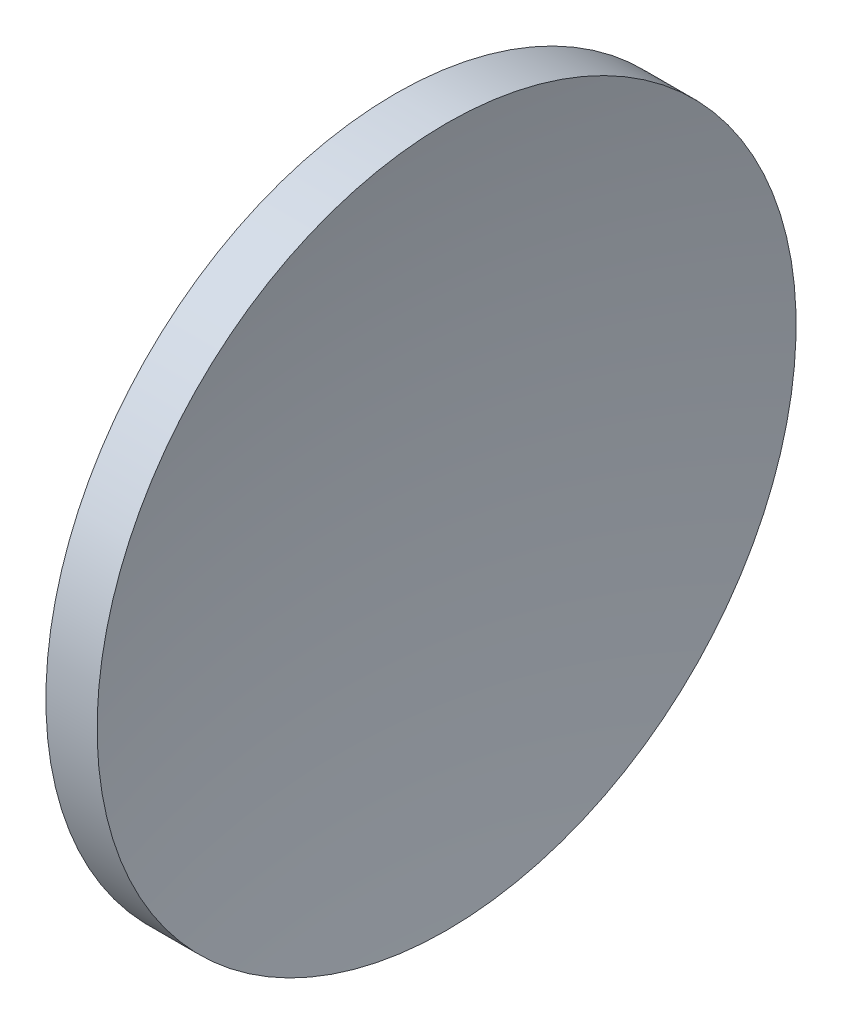
SolidWorks part; units mm, degrees
ref_plane "前视基准面" through (0, 0, 0) normal (0, 0, 1) x (1, 0, 0)
ref_plane "上视基准面" through (0, 0, 0) normal (0, 1, 0) x (1, 0, 0)
ref_plane "右视基准面" through (0, 0, 0) normal (1, 0, 0) x (0, 0, -1)
sketch "草图1" plane through (0, 0, 0) normal (0, 0, 1) x (1, 0, 0)
  line L0 (231.889, 130.4337) -> (271.8964, 130.4337) construction
  line L1 (249.1079, 155.4337) -> (252.7707, 155.4337)
  line L2 (245.199, 130.4337) -> (250.199, 130.4337)
  arc A0 (249.1079, 155.4337) -> (245.199, 130.4337) centre (327.099, 130.4337) ccw
  arc A1 (252.7707, 155.4337) -> (250.199, 130.4337) centre (372.999, 130.4337) ccw
revolve "旋转1" add sketch "草图1" angle 360 about L0
